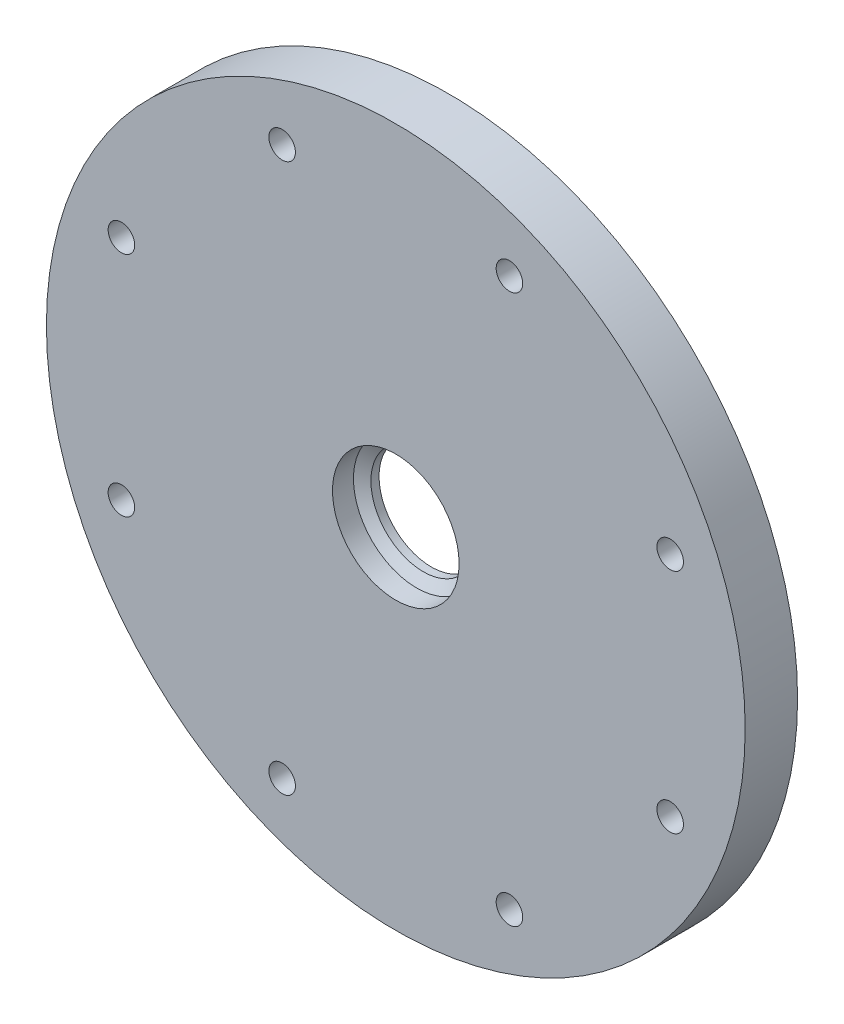
SolidWorks part; units mm, degrees
material "6061-T6 (SS)"
ref_plane "Front Plane" through (0, 0, 0) normal (0, 0, 1) x (1, 0, 0)
ref_plane "Top Plane" through (0, 0, 0) normal (0, 1, 0) x (1, 0, 0)
ref_plane "Right Plane" through (0, 0, 0) normal (1, 0, 0) x (0, 0, -1)
sketch "Sketch1" plane through (0, 0, 0) normal (0, 0, 1) x (1, 0, 0)
  circle A0 centre (0, 0) radius 9.525
  circle A2 centre (0, 0) radius 63.5
  dimension "D1" = 127
  dimension "D3" = 19.05
extrude "Boss-Extrude1" add sketch "Sketch1" along normal blind 9.525
sketch "Sketch4" plane through (0, 0, 9.525) normal (0, 0, 1) x (1, 0, 0)
  line L0 (49.8664, 20.6553) -> (58.6664, 24.3004) construction
  line L1 (0, 0) -> (63.5, 0) construction
  circle A0 centre (49.8664, 20.6553) radius 2.413
  circle A1 centre (0, 0) radius 63.5 construction
  dimension "D1" = 4.826
  dimension "D2" = 9.525
  dimension "D3" = 22.5
extrude "Cut-Extrude1" cut sketch "Sketch4" against normal through all
pattern_circular "CirPattern1" count 8 over 360 about axis through (0, 0, 0) along (0, 0, 1) of "Cut-Extrude1"
curve "Curve1"
  spline degree 3 poles (34.2959, 0, 0) (34.2988, 0.0719, 0) (34.3048, 0.2158, 0) (34.312, 0.4316, 0) (34.3179, 0.6476, 0) (34.3225, 0.8637, 0) (34.3258, 1.0798, 0) (34.3277, 1.296, 0) (34.3283, 1.5123, 0) (34.3275, 1.7287, 0) (34.3253, 1.9451, 0) (34.3218, 2.1615, 0) (34.317, 2.378, 0) (34.3108, 2.5945, 0) (34.3032, 2.811, 0) (34.2943, 3.0275, 0) (34.284, 3.2441, 0) (34.2724, 3.4606, 0) (34.2594, 3.6771, 0) (34.245, 3.8936, 0) (34.2293, 4.11, 0) (34.2122, 4.3264, 0) (34.1938, 4.5427, 0) (34.174, 4.759, 0) (34.1528, 4.9752, 0) (34.1303, 5.1914, 0) (34.1064, 5.4074, 0) (34.0811, 5.6234, 0) (34.0545, 5.8392, 0) (34.0265, 6.055, 0) (33.9972, 6.2706, 0) (33.9665, 6.4861, 0) (33.9344, 6.7015, 0) (33.901, 6.9167, 0) (33.8662, 7.1317, 0) (33.8301, 7.3466, 0) (33.7926, 7.5614, 0) (33.7537, 7.7759, 0) (33.7135, 7.9903, 0) (33.6719, 8.2044, 0) (33.629, 8.4184, 0) (33.5847, 8.6321, 0) (33.5391, 8.8456, 0) (33.4921, 9.0589, 0) (33.4438, 9.272, 0) (33.3941, 9.4848, 0) (33.343, 9.6973, 0) (33.2906, 9.9096, 0) (33.2369, 10.1216, 0) (33.1818, 10.3333, 0) (33.1254, 10.5447, 0) (33.0676, 10.7558, 0) (33.0085, 10.9666, 0) (32.9481, 11.1772, 0) (32.8863, 11.3873, 0) (32.8232, 11.5972, 0) (32.7587, 11.8067, 0) (32.6929, 12.0158, 0) (32.6258, 12.2246, 0) (32.5573, 12.433, 0) (32.4875, 12.6411, 0) (32.4164, 12.8487, 0) (32.344, 13.056, 0) (32.2702, 13.2629, 0) (32.1952, 13.4693, 0) (32.1188, 13.6754, 0) (32.0411, 13.881, 0) (31.9621, 14.0862, 0) (31.8817, 14.2909, 0) (31.8001, 14.4952, 0) (31.7172, 14.699, 0) (31.6329, 14.9023, 0) (31.5474, 15.1052, 0) (31.4605, 15.3076, 0) (31.3724, 15.5095, 0) (31.283, 15.7109, 0) (31.1923, 15.9118, 0) (31.1002, 16.1122, 0) (31.007, 16.312, 0) (30.9124, 16.5113, 0) (30.8165, 16.7101, 0) (30.7194, 16.9083, 0) (30.621, 17.1059, 0) (30.5214, 17.303, 0) (30.4205, 17.4995, 0) (30.3183, 17.6955, 0) (30.2148, 17.8908, 0) (30.1101, 18.0856, 0) (30.0042, 18.2797, 0) (29.897, 18.4732, 0) (29.7885, 18.6661, 0) (29.6788, 18.8583, 0) (29.5679, 19.05, 0) (29.4557, 19.2409, 0) (29.3424, 19.4313, 0) (29.2277, 19.6209, 0) (29.1119, 19.8099, 0) (28.9949, 19.9982, 0) (28.8766, 20.1858, 0) (28.7571, 20.3727, 0) (28.6364, 20.5589, 0) (28.5145, 20.7444, 0) (28.3914, 20.9292, 0) (28.2671, 21.1133, 0) (28.1417, 21.2966, 0) (28.015, 21.4792, 0) (27.8872, 21.661, 0) (27.7582, 21.8421, 0) (27.628, 22.0224, 0) (27.4966, 22.202, 0) (27.3641, 22.3807, 0) (27.2304, 22.5587, 0) (27.0956, 22.7359, 0) (26.9596, 22.9123, 0) (26.8225, 23.0879, 0) (26.6842, 23.2626, 0) (26.5448, 23.4365, 0) (26.4043, 23.6096, 0) (26.2626, 23.7819, 0) (26.1198, 23.9533, 0) (25.9759, 24.1239, 0) (25.8309, 24.2936, 0) (25.6848, 24.4624, 0) (25.5376, 24.6304, 0) (25.3893, 24.7974, 0) (25.2399, 24.9636, 0) (25.0894, 25.1289, 0) (24.9379, 25.2933, 0) (24.7852, 25.4568, 0) (24.6315, 25.6193, 0) (24.4768, 25.781, 0) (24.3209, 25.9417, 0) (24.1641, 26.1014, 0) (24.0062, 26.2602, 0) (23.8472, 26.4181, 0) (23.6872, 26.575, 0) (23.5262, 26.7309, 0) (23.3641, 26.8859, 0) (23.2011, 27.0399, 0) (23.037, 27.1929, 0) (22.8719, 27.3449, 0) (22.7058, 27.4959, 0) (22.5388, 27.6459, 0) (22.3707, 27.7949, 0) (22.2017, 27.9429, 0) (22.0317, 28.0899, 0) (21.8607, 28.2358, 0) (21.6887, 28.3806, 0) (21.5158, 28.5245, 0) (21.342, 28.6673, 0) (21.1672, 28.809, 0) (20.9915, 28.9497, 0) (20.8148, 29.0893, 0) (20.6372, 29.2278, 0) (20.4587, 29.3652, 0) (20.2793, 29.5016, 0) (20.099, 29.6368, 0) (19.9177, 29.771, 0) (19.7356, 29.9041, 0) (19.5526, 30.036, 0) (19.3688, 30.1668, 0) (19.184, 30.2965, 0) (18.9984, 30.4251, 0) (18.8119, 30.5526, 0) (18.6246, 30.6789, 0) (18.4365, 30.804, 0) (18.2475, 30.928, 0) (18.0576, 31.0509, 0) (17.867, 31.1725, 0) (17.6755, 31.2931, 0) (17.4833, 31.4124, 0) (17.2902, 31.5306, 0) (17.0963, 31.6475, 0) (16.9017, 31.7633, 0) (16.7062, 31.8779, 0) (16.51, 31.9913, 0) (16.3131, 32.1035, 0) (16.1153, 32.2145, 0) (15.9169, 32.3243, 0) (15.7176, 32.4328, 0) (15.5177, 32.5401, 0) (15.317, 32.6462, 0) (15.1156, 32.7511, 0) (14.9135, 32.8547, 0) (14.7107, 32.957, 0) (14.5072, 33.0582, 0) (14.303, 33.158, 0) (14.0981, 33.2566, 0) (13.8925, 33.354, 0) (13.6863, 33.4501, 0) (13.4794, 33.5449, 0) (13.2719, 33.6384, 0) (13.0637, 33.7306, 0) (12.8549, 33.8216, 0) (12.6455, 33.9112, 0) (12.4354, 33.9996, 0) (12.2247, 34.0867, 0) (12.0135, 34.1724, 0) (11.8016, 34.2569, 0) (11.5892, 34.3401, 0) (11.3761, 34.4219, 0) (11.1625, 34.5024, 0) (10.9484, 34.5816, 0) (10.7337, 34.6595, 0) (10.5184, 34.736, 0) (10.3026, 34.8112, 0) (10.0863, 34.885, 0) (9.8694, 34.9576, 0) (9.6521, 35.0287, 0) (9.4342, 35.0986, 0) (9.2158, 35.167, 0) (8.997, 35.2341, 0) (8.7777, 35.2999, 0) (8.5579, 35.3643, 0) (8.3376, 35.4273, 0) (8.1169, 35.4889, 0) (7.8957, 35.5492, 0) (7.6741, 35.6081, 0) (7.4521, 35.6656, 0) (7.2297, 35.7218, 0) (7.0068, 35.7765, 0) (6.7835, 35.8299, 0) (6.5599, 35.8819, 0) (6.3359, 35.9325, 0) (6.1114, 35.9817, 0) (5.8867, 36.0294, 0) (5.6615, 36.0758, 0) (5.436, 36.1208, 0) (5.2102, 36.1644, 0) (4.984, 36.2065, 0) (4.7575, 36.2473, 0) (4.5307, 36.2866, 0) (4.3036, 36.3245, 0) (4.0762, 36.361, 0) (3.8485, 36.3961, 0) (3.6205, 36.4297, 0) (3.3923, 36.462, 0) (3.1638, 36.4928, 0) (2.935, 36.5221, 0) (2.706, 36.55, 0) (2.4768, 36.5765, 0) (2.2473, 36.6016, 0) (2.0176, 36.6252, 0) (1.7877, 36.6474, 0) (1.5576, 36.6682, 0) (1.3274, 36.6875, 0) (1.0969, 36.7053, 0) (0.8663, 36.7217, 0) (0.6355, 36.7367, 0) (0.4045, 36.7502, 0) (0.1734, 36.7623, 0) (-0.0578, 36.7729, 0) (-0.2892, 36.782, 0) (-0.5207, 36.7897, 0) (-0.7523, 36.796, 0) (-0.9839, 36.8008, 0) (-1.2157, 36.8041, 0) (-1.4476, 36.806, 0) (-1.6795, 36.8064, 0) (-1.9115, 36.8054, 0) (-2.1435, 36.8029, 0) (-2.3756, 36.7989, 0) (-2.6077, 36.7935, 0) (-2.8399, 36.7866, 0) (-3.0721, 36.7783, 0) (-3.3042, 36.7684, 0) (-3.5364, 36.7572, 0) (-3.7686, 36.7444, 0) (-4.0007, 36.7302, 0) (-4.2328, 36.7145, 0) (-4.4649, 36.6974, 0) (-4.6969, 36.6788, 0) (-4.9289, 36.6587, 0) (-5.1608, 36.6372, 0) (-5.3926, 36.6142, 0) (-5.6243, 36.5897, 0) (-5.856, 36.5638, 0) (-6.0875, 36.5364, 0) (-6.319, 36.5076, 0) (-6.5503, 36.4772, 0) (-6.7815, 36.4455, 0) (-7.0125, 36.4122, 0) (-7.2434, 36.3775, 0) (-7.4741, 36.3413, 0) (-7.7047, 36.3037, 0) (-7.935, 36.2646, 0) (-8.1652, 36.224, 0) (-8.3952, 36.182, 0) (-8.625, 36.1385, 0) (-8.8546, 36.0936, 0) (-9.084, 36.0472, 0) (-9.3131, 35.9994, 0) (-9.542, 35.9501, 0) (-9.7706, 35.8993, 0) (-9.999, 35.8471, 0) (-10.2271, 35.7934, 0) (-10.4549, 35.7383, 0) (-10.6824, 35.6818, 0) (-10.9097, 35.6238, 0) (-11.1366, 35.5643, 0) (-11.3632, 35.5034, 0) (-11.5895, 35.4411, 0) (-11.8155, 35.3773, 0) (-12.0411, 35.3121, 0) (-12.2663, 35.2455, 0) (-12.4912, 35.1774, 0) (-12.7157, 35.1079, 0) (-12.9399, 35.0369, 0) (-13.1637, 34.9645, 0) (-13.387, 34.8907, 0) (-13.61, 34.8155, 0) (-13.8325, 34.7388, 0) (-14.0546, 34.6608, 0) (-14.2763, 34.5813, 0) (-14.4975, 34.5004, 0) (-14.7183, 34.418, 0) (-14.9386, 34.3343, 0) (-15.1585, 34.2492, 0) (-15.3778, 34.1626, 0) (-15.5967, 34.0747, 0) (-15.8151, 33.9853, 0) (-16.033, 33.8945, 0) (-16.2503, 33.8024, 0) (-16.4672, 33.7089, 0) (-16.6835, 33.6139, 0) (-16.8992, 33.5176, 0) (-17.1145, 33.4199, 0) (-17.3291, 33.3208, 0) (-17.5432, 33.2204, 0) (-17.7567, 33.1186, 0) (-17.9696, 33.0154, 0) (-18.1819, 32.9108, 0) (-18.3937, 32.8049, 0) (-18.6048, 32.6976, 0) (-18.8153, 32.5889, 0) (-19.0251, 32.479, 0) (-19.2343, 32.3676, 0) (-19.4429, 32.2549, 0) (-19.6508, 32.1409, 0) (-19.8581, 32.0255, 0) (-20.0646, 31.9088, 0) (-20.2705, 31.7908, 0) (-20.4757, 31.6714, 0) (-20.6802, 31.5507, 0) (-20.884, 31.4287, 0) (-21.0871, 31.3054, 0) (-21.2895, 31.1808, 0) (-21.4911, 31.0548, 0) (-21.692, 30.9276, 0) (-21.8921, 30.7991, 0) (-22.0915, 30.6692, 0) (-22.2901, 30.5381, 0) (-22.488, 30.4057, 0) (-22.685, 30.272, 0) (-22.8813, 30.1371, 0) (-23.0767, 30.0009, 0) (-23.2714, 29.8634, 0) (-23.4652, 29.7246, 0) (-23.6583, 29.5846, 0) (-23.8504, 29.4434, 0) (-24.0418, 29.3008, 0) (-24.2323, 29.1571, 0) (-24.4219, 29.0121, 0) (-24.6107, 28.8659, 0) (-24.7986, 28.7185, 0) (-24.9856, 28.5698, 0) (-25.1718, 28.4199, 0) (-25.357, 28.2689, 0) (-25.5413, 28.1166, 0) (-25.7247, 27.9631, 0) (-25.9073, 27.8084, 0) (-26.0888, 27.6525, 0) (-26.2695, 27.4955, 0) (-26.4492, 27.3372, 0) (-26.6279, 27.1778, 0) (-26.8057, 27.0173, 0) (-26.9825, 26.8555, 0) (-27.1584, 26.6927, 0) (-27.3333, 26.5286, 0) (-27.5071, 26.3634, 0) (-27.68, 26.1971, 0) (-27.8519, 26.0297, 0) (-28.0228, 25.8611, 0) (-28.1926, 25.6914, 0) (-28.3615, 25.5206, 0) (-28.5293, 25.3487, 0) (-28.696, 25.1757, 0) (-28.8618, 25.0016, 0) (-29.0264, 24.8264, 0) (-29.19, 24.6502, 0) (-29.3525, 24.4728, 0) (-29.514, 24.2944, 0) (-29.6744, 24.1149, 0) (-29.8337, 23.9344, 0) (-29.9918, 23.7528, 0) (-30.1489, 23.5702, 0) (-30.3049, 23.3865, 0) (-30.4598, 23.2018, 0) (-30.6135, 23.0161, 0) (-30.7661, 22.8294, 0) (-30.9176, 22.6417, 0) (-31.0679, 22.4529, 0) (-31.2171, 22.2632, 0) (-31.3651, 22.0725, 0) (-31.512, 21.8808, 0) (-31.6576, 21.6881, 0) (-31.8021, 21.4945, 0) (-31.9455, 21.2999, 0) (-32.0876, 21.1043, 0) (-32.2286, 20.9079, 0) (-32.3683, 20.7104, 0) (-32.5068, 20.5121, 0) (-32.6442, 20.3128, 0) (-32.7803, 20.1126, 0) (-32.9151, 19.9115, 0) (-33.0488, 19.7095, 0) (-33.1812, 19.5066, 0) (-33.3124, 19.3028, 0) (-33.4423, 19.0981, 0) (-33.5709, 18.8926, 0) (-33.6983, 18.6862, 0) (-33.8244, 18.4789, 0) (-33.9493, 18.2709, 0) (-34.0729, 18.0619, 0) (-34.1952, 17.8522, 0) (-34.3162, 17.6416, 0) (-34.4359, 17.4302, 0) (-34.5543, 17.2179, 0) (-34.6714, 17.0049, 0) (-34.7872, 16.7911, 0) (-34.9017, 16.5765, 0) (-35.0148, 16.3612, 0) (-35.1266, 16.1451, 0) (-35.2371, 15.9282, 0) (-35.3463, 15.7105, 0) (-35.4541, 15.4922, 0) (-35.5606, 15.273, 0) (-35.6657, 15.0532, 0) (-35.7694, 14.8326, 0) (-35.8718, 14.6114, 0) (-35.9728, 14.3894, 0) (-36.0725, 14.1667, 0) (-36.1708, 13.9434, 0) (-36.2677, 13.7194, 0) (-36.3632, 13.4947, 0) (-36.4573, 13.2694, 0) (-36.55, 13.0434, 0) (-36.6413, 12.8167, 0) (-36.7312, 12.5895, 0) (-36.8198, 12.3616, 0) (-36.9069, 12.1331, 0) (-36.9925, 11.9039, 0) (-37.0768, 11.6742, 0) (-37.1596, 11.4439, 0) (-37.241, 11.2131, 0) (-37.321, 10.9816, 0) (-37.3996, 10.7496, 0) (-37.4766, 10.517, 0) (-37.5523, 10.2839, 0) (-37.6265, 10.0503, 0) (-37.6993, 9.8161, 0) (-37.7705, 9.5814, 0) (-37.8404, 9.3462, 0) (-37.9088, 9.1105, 0) (-37.9757, 8.8743, 0) (-38.0411, 8.6377, 0) (-38.105, 8.4005, 0) (-38.1675, 8.1629, 0) (-38.2285, 7.9249, 0) (-38.2881, 7.6864, 0) (-38.3461, 7.4475, 0) (-38.4026, 7.2081, 0) (-38.4577, 6.9683, 0) (-38.5112, 6.7281, 0) (-38.5633, 6.4876, 0) (-38.6138, 6.2466, 0) (-38.6629, 6.0052, 0) (-38.7104, 5.7635, 0) (-38.7565, 5.5214, 0) (-38.801, 5.279, 0) (-38.844, 5.0362, 0) (-38.8855, 4.7931, 0) (-38.9254, 4.5497, 0) (-38.9639, 4.306, 0) (-39.0008, 4.0619, 0) (-39.0362, 3.8176, 0) (-39.0701, 3.573, 0) (-39.1024, 3.3281, 0) (-39.1332, 3.0829, 0) (-39.1624, 2.8375, 0) (-39.1902, 2.5919, 0) (-39.2163, 2.346, 0) (-39.241, 2.0998, 0) (-39.2641, 1.8535, 0) (-39.2856, 1.6069, 0) (-39.3056, 1.3602, 0) (-39.3241, 1.1133, 0) (-39.341, 0.8661, 0) (-39.3564, 0.6189, 0) (-39.3702, 0.3714, 0) (-39.3824, 0.1238, 0) (-39.3931, -0.1239, 0) (-39.4022, -0.3718, 0) (-39.4098, -0.6197, 0) (-39.4158, -0.8678, 0) (-39.4203, -1.116, 0) (-39.4232, -1.3643, 0) (-39.4245, -1.6126, 0) (-39.4243, -1.8611, 0) (-39.4225, -2.1096, 0) (-39.4191, -2.3581, 0) (-39.4142, -2.6067, 0) (-39.4077, -2.8553, 0) (-39.3996, -3.1039, 0) (-39.39, -3.3526, 0) (-39.3788, -3.6012, 0) (-39.366, -3.8499, 0) (-39.3517, -4.0985, 0) (-39.3358, -4.3471, 0) (-39.3183, -4.5957, 0) (-39.2993, -4.8442, 0) (-39.2787, -5.0926, 0) (-39.2565, -5.341, 0) (-39.2327, -5.5893, 0) (-39.2074, -5.8375, 0) (-39.1805, -6.0857, 0) (-39.1521, -6.3337, 0) (-39.122, -6.5816, 0) (-39.0904, -6.8294, 0) (-39.0573, -7.077, 0) (-39.0225, -7.3245, 0) (-38.9862, -7.5718, 0) (-38.9484, -7.819, 0) (-38.9089, -8.066, 0) (-38.8679, -8.3128, 0) (-38.8254, -8.5594, 0) (-38.7813, -8.8058, 0) (-38.7356, -9.0519, 0) (-38.6883, -9.2979, 0) (-38.6395, -9.5436, 0) (-38.5891, -9.7891, 0) (-38.5372, -10.0343, 0) (-38.4837, -10.2793, 0) (-38.4287, -10.524, 0) (-38.3721, -10.7683, 0) (-38.314, -11.0124, 0) (-38.2543, -11.2562, 0) (-38.193, -11.4997, 0) (-38.1302, -11.7429, 0) (-38.0659, -11.9857, 0) (-38, -12.2282, 0) (-37.9325, -12.4703, 0) (-37.8636, -12.712, 0) (-37.7931, -12.9534, 0) (-37.721, -13.1944, 0) (-37.6474, -13.435, 0) (-37.5723, -13.6752, 0) (-37.4956, -13.915, 0) (-37.4175, -14.1544, 0) (-37.3378, -14.3933, 0) (-37.2565, -14.6318, 0) (-37.1738, -14.8698, 0) (-37.0895, -15.1074, 0) (-37.0037, -15.3445, 0) (-36.9164, -15.5811, 0) (-36.8276, -15.8173, 0) (-36.7373, -16.0529, 0) (-36.6454, -16.288, 0) (-36.5521, -16.5226, 0) (-36.4573, -16.7567, 0) (-36.3609, -16.9902, 0) (-36.2631, -17.2232, 0) (-36.1638, -17.4556, 0) (-36.063, -17.6875, 0) (-35.9607, -17.9188, 0) (-35.8569, -18.1495, 0) (-35.7517, -18.3796, 0) (-35.6449, -18.6091, 0) (-35.5367, -18.8379, 0) (-35.4271, -19.0662, 0) (-35.3159, -19.2938, 0) (-35.2034, -19.5208, 0) (-35.0893, -19.7471, 0) (-34.9738, -19.9728, 0) (-34.8569, -20.1978, 0) (-34.7385, -20.4221, 0) (-34.6186, -20.6457, 0) (-34.4973, -20.8686, 0) (-34.3746, -21.0908, 0) (-34.2505, -21.3123, 0) (-34.1249, -21.5331, 0) (-33.9979, -21.7531, 0) (-33.8695, -21.9724, 0) (-33.7397, -22.191, 0) (-33.6085, -22.4087, 0) (-33.4758, -22.6257, 0) (-33.3418, -22.842, 0) (-33.2064, -23.0574, 0) (-33.0696, -23.272, 0) (-32.9314, -23.4858, 0) (-32.7918, -23.6988, 0) (-32.6508, -23.911, 0) (-32.5085, -24.1224, 0) (-32.3648, -24.3328, 0) (-32.2198, -24.5425, 0) (-32.0734, -24.7513, 0) (-31.9256, -24.9592, 0) (-31.7765, -25.1662, 0) (-31.626, -25.3724, 0) (-31.4743, -25.5776, 0) (-31.3211, -25.782, 0) (-31.1667, -25.9854, 0) (-31.0109, -26.1879, 0) (-30.8539, -26.3895, 0) (-30.6955, -26.5901, 0) (-30.5358, -26.7898, 0) (-30.3748, -26.9886, 0) (-30.2126, -27.1863, 0) (-30.049, -27.3831, 0) (-29.8842, -27.5789, 0) (-29.7181, -27.7738, 0) (-29.5507, -27.9676, 0) (-29.382, -28.1604, 0) (-29.2122, -28.3522, 0) (-29.041, -28.543, 0) (-28.8686, -28.7328, 0) (-28.695, -28.9215, 0) (-28.5201, -29.1092, 0) (-28.3441, -29.2958, 0) (-28.1668, -29.4813, 0) (-27.9882, -29.6658, 0) (-27.8085, -29.8492, 0) (-27.6276, -30.0315, 0) (-27.4455, -30.2128, 0) (-27.2622, -30.3929, 0) (-27.0777, -30.5719, 0) (-26.8921, -30.7498, 0) (-26.7053, -30.9266, 0) (-26.5173, -31.1022, 0) (-26.3282, -31.2767, 0) (-26.1379, -31.45, 0) (-25.9465, -31.6222, 0) (-25.7539, -31.7933, 0) (-25.5603, -31.9631, 0) (-25.3655, -32.1318, 0) (-25.1696, -32.2993, 0) (-24.9726, -32.4656, 0) (-24.7745, -32.6307, 0) (-24.5753, -32.7946, 0) (-24.3751, -32.9573, 0) (-24.1737, -33.1188, 0) (-23.9713, -33.279, 0) (-23.7679, -33.438, 0) (-23.5634, -33.5958, 0) (-23.3578, -33.7523, 0) (-23.1512, -33.9075, 0) (-22.9436, -34.0615, 0) (-22.735, -34.2142, 0) (-22.5253, -34.3657, 0) (-22.3147, -34.5158, 0) (-22.103, -34.6647, 0) (-21.8904, -34.8123, 0) (-21.6767, -34.9586, 0) (-21.4621, -35.1035, 0) (-21.2466, -35.2472, 0) (-21.03, -35.3895, 0) (-20.8126, -35.5305, 0) (-20.5942, -35.6702, 0) (-20.3748, -35.8085, 0) (-20.1545, -35.9454, 0) (-19.9334, -36.0811, 0) (-19.7113, -36.2153, 0) (-19.4883, -36.3482, 0) (-19.2644, -36.4797, 0) (-19.0396, -36.6099, 0) (-18.814, -36.7387, 0) (-18.5874, -36.866, 0) (-18.3601, -36.992, 0) (-18.1319, -37.1166, 0) (-17.9028, -37.2398, 0) (-17.6729, -37.3615, 0) (-17.4422, -37.4819, 0) (-17.2107, -37.6008, 0) (-16.9783, -37.7183, 0) (-16.7452, -37.8343, 0) (-16.5113, -37.9489, 0) (-16.2766, -38.0621, 0) (-16.0411, -38.1738, 0) (-15.8049, -38.2841, 0) (-15.5679, -38.3929, 0) (-15.3302, -38.5002, 0) (-15.0917, -38.6061, 0) (-14.8526, -38.7105, 0) (-14.6127, -38.8134, 0) (-14.3721, -38.9148, 0) (-14.1308, -39.0147, 0) (-13.8888, -39.1132, 0) (-13.6461, -39.2101, 0) (-13.4028, -39.3056, 0) (-13.1588, -39.3995, 0) (-12.9141, -39.4919, 0) (-12.6688, -39.5828, 0) (-12.4229, -39.6722, 0) (-12.1764, -39.76, 0) (-11.9292, -39.8463, 0) (-11.6814, -39.9311, 0) (-11.4331, -40.0143, 0) (-11.1841, -40.096, 0) (-10.9346, -40.1762, 0) (-10.6845, -40.2548, 0) (-10.4339, -40.3318, 0) (-10.1827, -40.4073, 0) (-9.931, -40.4812, 0) (-9.6787, -40.5536, 0) (-9.426, -40.6244, 0) (-9.1727, -40.6936, 0) (-8.9189, -40.7612, 0) (-8.6647, -40.8272, 0) (-8.4099, -40.8917, 0) (-8.1547, -40.9546, 0) (-7.8991, -41.0159, 0) (-7.643, -41.0755, 0) (-7.3864, -41.1336, 0) (-7.1294, -41.1901, 0) (-6.872, -41.245, 0) (-6.6142, -41.2983, 0) (-6.356, -41.3499, 0) (-6.0974, -41.4, 0) (-5.8385, -41.4484, 0) (-5.5791, -41.4952, 0) (-5.3194, -41.5404, 0) (-5.0594, -41.584, 0) (-4.799, -41.6259, 0) (-4.5383, -41.6663, 0) (-4.2773, -41.7049, 0) (-4.016, -41.742, 0) (-3.7543, -41.7774, 0) (-3.4924, -41.8112, 0) (-3.2302, -41.8433, 0) (-2.9678, -41.8738, 0) (-2.7051, -41.9026, 0) (-2.4421, -41.9298, 0) (-2.1789, -41.9554, 0) (-1.9155, -41.9793, 0) (-1.6519, -42.0015, 0) (-1.3881, -42.0221, 0) (-1.124, -42.041, 0) (-0.8598, -42.0583, 0) (-0.5954, -42.0739, 0) (-0.3309, -42.0878, 0) (-0.0662, -42.1001, 0) (0.1987, -42.1108, 0) (0.4636, -42.1197, 0) (0.7287, -42.127, 0) (0.9939, -42.1326, 0) (1.2592, -42.1366, 0) (1.5246, -42.1389, 0) (1.7901, -42.1395, 0) (2.0556, -42.1384, 0) (2.3212, -42.1357, 0) (2.5868, -42.1313, 0) (2.8525, -42.1252, 0) (3.1182, -42.1175, 0) (3.3839, -42.1081, 0) (3.6497, -42.097, 0) (3.9154, -42.0842, 0) (4.1811, -42.0697, 0) (4.4468, -42.0536, 0) (4.7124, -42.0358, 0) (4.978, -42.0163, 0) (5.2435, -41.9952, 0) (5.509, -41.9723, 0) (5.7744, -41.9478, 0) (6.0397, -41.9216, 0) (6.3049, -41.8938, 0) (6.5699, -41.8642, 0) (6.8349, -41.833, 0) (7.0997, -41.8001, 0) (7.3644, -41.7655, 0) (7.6289, -41.7293, 0) (7.8933, -41.6914, 0) (8.1575, -41.6518, 0) (8.4215, -41.6105, 0) (8.6853, -41.5676, 0) (8.9489, -41.5229, 0) (9.2123, -41.4767, 0) (9.4754, -41.4287, 0) (9.7383, -41.3791, 0) (10.001, -41.3278, 0) (10.2634, -41.2748, 0) (10.5256, -41.2202, 0) (10.7874, -41.1639, 0) (11.049, -41.106, 0) (11.3102, -41.0464, 0) (11.5712, -40.9851, 0) (11.8318, -40.9222, 0) (12.0921, -40.8576, 0) (12.3521, -40.7914, 0) (12.6116, -40.7235, 0) (12.8709, -40.6539, 0) (13.1297, -40.5827, 0) (13.3882, -40.5099, 0) (13.6463, -40.4354, 0) (13.9039, -40.3593, 0) (14.1612, -40.2815, 0) (14.418, -40.2021, 0) (14.6744, -40.1211, 0) (14.9303, -40.0384, 0) (15.1858, -39.9541, 0) (15.4408, -39.8682, 0) (15.6953, -39.7806, 0) (15.9493, -39.6914, 0) (16.2029, -39.6006, 0) (16.4559, -39.5082, 0) (16.7084, -39.4141, 0) (16.9604, -39.3185, 0) (17.2118, -39.2212, 0) (17.4627, -39.1224, 0) (17.713, -39.0219, 0) (17.9627, -38.9198, 0) (18.2119, -38.8161, 0) (18.4604, -38.7109, 0) (18.7084, -38.604, 0) (18.9557, -38.4956, 0) (19.2024, -38.3856, 0) (19.4485, -38.274, 0) (19.694, -38.1608, 0) (19.9388, -38.046, 0) (20.1829, -37.9297, 0) (20.4263, -37.8118, 0) (20.6691, -37.6924, 0) (20.9112, -37.5714, 0) (21.1526, -37.4488, 0) (21.3932, -37.3247, 0) (21.6331, -37.199, 0) (21.8723, -37.0718, 0) (22.1108, -36.9431, 0) (22.3485, -36.8128, 0) (22.5854, -36.6811, 0) (22.8216, -36.5477, 0) (23.057, -36.4129, 0) (23.2916, -36.2766, 0) (23.5253, -36.1387, 0) (23.7583, -35.9993, 0) (23.9905, -35.8585, 0) (24.2218, -35.7161, 0) (24.4523, -35.5723, 0) (24.6819, -35.4269, 0) (24.9107, -35.2801, 0) (25.1386, -35.1318, 0) (25.3656, -34.982, 0) (25.5917, -34.8308, 0) (25.8169, -34.6781, 0) (26.0412, -34.524, 0) (26.2647, -34.3684, 0) (26.4871, -34.2114, 0) (26.7087, -34.0529, 0) (26.9293, -33.893, 0) (27.1489, -33.7316, 0) (27.3676, -33.5689, 0) (27.5853, -33.4047, 0) (27.802, -33.2391, 0) (28.0178, -33.0722, 0) (28.2325, -32.9038, 0) (28.4462, -32.734, 0) (28.6589, -32.5628, 0) (28.8706, -32.3903, 0) (29.0812, -32.2164, 0) (29.2908, -32.0411, 0) (29.4994, -31.8644, 0) (29.7068, -31.6864, 0) (29.9133, -31.5071, 0) (30.1186, -31.3264, 0) (30.3228, -31.1444, 0) (30.526, -30.961, 0) (30.728, -30.7763, 0) (30.9289, -30.5903, 0) (31.1287, -30.403, 0) (31.3274, -30.2144, 0) (31.5249, -30.0245, 0) (31.7213, -29.8333, 0) (31.9165, -29.6409, 0) (32.1105, -29.4471, 0) (32.3034, -29.2521, 0) (32.4951, -29.0558, 0) (32.6856, -28.8583, 0) (32.8749, -28.6595, 0) (33.063, -28.4595, 0) (33.2499, -28.2582, 0) (33.4356, -28.0558, 0) (33.62, -27.8521, 0) (33.8032, -27.6472, 0) (33.9851, -27.4411, 0) (34.1658, -27.2338, 0) (34.3452, -27.0253, 0) (34.5234, -26.8156, 0) (34.7003, -26.6048, 0) (34.8759, -26.3928, 0) (35.0502, -26.1796, 0) (35.2232, -25.9653, 0) (35.3949, -25.7499, 0) (35.5652, -25.5333, 0) (35.7343, -25.3156, 0) (35.902, -25.0968, 0) (36.0684, -24.8769, 0) (36.2334, -24.6558, 0) (36.3971, -24.4337, 0) (36.5594, -24.2105, 0) (36.7204, -23.9863, 0) (36.8799, -23.7609, 0) (37.0381, -23.5345, 0) (37.195, -23.3071, 0) (37.3504, -23.0786, 0) (37.5044, -22.8491, 0) (37.657, -22.6185, 0) (37.8082, -22.387, 0) (37.9579, -22.1544, 0) (38.1063, -21.9208, 0) (38.2532, -21.6863, 0) (38.3986, -21.4508, 0) (38.5426, -21.2142, 0) (38.6852, -20.9768, 0) (38.8263, -20.7384, 0) (38.9659, -20.499, 0) (39.1041, -20.2587, 0) (39.2407, -20.0175, 0) (39.3759, -19.7753, 0) (39.5096, -19.5323, 0) (39.6418, -19.2883, 0) (39.7725, -19.0435, 0) (39.9017, -18.7977, 0) (40.0293, -18.5511, 0) (40.1554, -18.3037, 0) (40.2801, -18.0554, 0) (40.4031, -17.8062, 0) (40.5247, -17.5562, 0) (40.6446, -17.3054, 0) (40.7631, -17.0538, 0) (40.88, -16.8014, 0) (40.9953, -16.5482, 0) (41.109, -16.2941, 0) (41.2212, -16.0394, 0) (41.3318, -15.7838, 0) (41.4408, -15.5275, 0) (41.5482, -15.2704, 0) (41.6541, -15.0127, 0) (41.7583, -14.7541, 0) (41.8609, -14.4949, 0) (41.9619, -14.235, 0) (42.0614, -13.9743, 0) (42.1591, -13.713, 0) (42.2553, -13.451, 0) (42.3499, -13.1883, 0) (42.4428, -12.925, 0) (42.534, -12.661, 0) (42.6237, -12.3964, 0) (42.7117, -12.1312, 0) (42.798, -11.8653, 0) (42.8827, -11.5988, 0) (42.9657, -11.3318, 0) (43.0471, -11.0641, 0) (43.1268, -10.7959, 0) (43.2048, -10.5271, 0) (43.2811, -10.2578, 0) (43.3558, -9.9879, 0) (43.4288, -9.7175, 0) (43.5001, -9.4466, 0) (43.5697, -9.1751, 0) (43.6376, -8.9032, 0) (43.7039, -8.6307, 0) (43.7684, -8.3578, 0) (43.8312, -8.0844, 0) (43.8923, -7.8106, 0) (43.9517, -7.5363, 0) (44.0094, -7.2615, 0) (44.0654, -6.9864, 0) (44.1197, -6.7108, 0) (44.1722, -6.4348, 0) (44.223, -6.1584, 0) (44.2721, -5.8816, 0) (44.3194, -5.6045, 0) (44.365, -5.327, 0) (44.4089, -5.0491, 0) (44.4511, -4.7709, 0) (44.4915, -4.4924, 0) (44.5301, -4.2136, 0) (44.567, -3.9344, 0) (44.6022, -3.655, 0) (44.6356, -3.3752, 0) (44.6672, -3.0952, 0) (44.6971, -2.8149, 0) (44.7252, -2.5344, 0) (44.7516, -2.2536, 0) (44.7762, -1.9726, 0) (44.7991, -1.6914, 0) (44.8202, -1.4099, 0) (44.8395, -1.1283, 0) (44.857, -0.8465, 0) (44.8728, -0.5645, 0) (44.8869, -0.2823, 0) (44.8948, -0.0941, 0) (44.8987, 0, 0) knots 0 0 0 0 0.00087 0.001741 0.002611 0.003482 0.004354 0.005225 0.006097 0.006969 0.007841 0.008713 0.009586 0.010459 0.011332 0.012205 0.013079 0.013953 0.014827 0.015701 0.016576 0.017451 0.018326 0.019201 0.020077 0.020952 0.021828 0.022705 0.023581 0.024458 0.025335 0.026212 0.02709 0.027968 0.028845 0.029724 0.030602 0.031481 0.03236 0.033239 0.034119 0.034998 0.035878 0.036758 0.037639 0.038519 0.0394 0.040282 0.041163 0.042045 0.042927 0.043809 0.044691 0.045574 0.046457 0.04734 0.048223 0.049107 0.049991 0.050875 0.051759 0.052644 0.053529 0.054414 0.055299 0.056185 0.057071 0.057957 0.058843 0.05973 0.060616 0.061504 0.062391 0.063278 0.064166 0.065054 0.065943 0.066831 0.06772 0.068609 0.069499 0.070388 0.071278 0.072168 0.073058 0.073949 0.07484 0.075731 0.076622 0.077514 0.078405 0.079298 0.08019 0.081082 0.081975 0.082868 0.083762 0.084655 0.085549 0.086443 0.087337 0.088232 0.089127 0.090022 0.090917 0.091813 0.092709 0.093605 0.094501 0.095398 0.096294 0.097191 0.098089 0.098986 0.099884 0.100782 0.101681 0.102579 0.103478 0.104377 0.105276 0.106176 0.107076 0.107976 0.108876 0.109777 0.110678 0.111579 0.11248 0.113382 0.114284 0.115186 0.116088 0.116991 0.117894 0.118797 0.1197 0.120604 0.121508 0.122412 0.123316 0.124221 0.125126 0.126031 0.126936 0.127842 0.128748 0.129654 0.130561 0.131467 0.132374 0.133281 0.134189 0.135096 0.136004 0.136913 0.137821 0.13873 0.139639 0.140548 0.141457 0.142367 0.143277 0.144187 0.145098 0.146009 0.14692 0.147831 0.148742 0.149654 0.150566 0.151478 0.152391 0.153304 0.154217 0.15513 0.156044 0.156957 0.157872 0.158786 0.1597 0.160615 0.16153 0.162446 0.163361 0.164277 0.165193 0.16611 0.167026 0.167943 0.16886 0.169778 0.170695 0.171613 0.172531 0.17345 0.174369 0.175287 0.176207 0.177126 0.178046 0.178966 0.179886 0.180806 0.181727 0.182648 0.183569 0.184491 0.185413 0.186335 0.187257 0.18818 0.189102 0.190025 0.190949 0.191872 0.192796 0.19372 0.194645 0.195569 0.196494 0.197419 0.198345 0.19927 0.200196 0.201122 0.202049 0.202975 0.203902 0.204829 0.205757 0.206685 0.207613 0.208541 0.209469 0.210398 0.211327 0.212256 0.213186 0.214116 0.215046 0.215976 0.216906 0.217837 0.218768 0.2197 0.220631 0.221563 0.222495 0.223428 0.22436 0.225293 0.226226 0.22716 0.228093 0.229027 0.229961 0.230896 0.231831 0.232766 0.233701 0.234636 0.235572 0.236508 0.237444 0.238381 0.239318 0.240255 0.241192 0.24213 0.243067 0.244006 0.244944 0.245883 0.246821 0.247761 0.2487 0.24964 0.25058 0.25152 0.25246 0.253401 0.254342 0.255283 0.256225 0.257166 0.258108 0.259051 0.259993 0.260936 0.261879 0.262822 0.263766 0.26471 0.265654 0.266598 0.267543 0.268488 0.269433 0.270378 0.271324 0.27227 0.273216 0.274163 0.275109 0.276056 0.277004 0.277951 0.278899 0.279847 0.280795 0.281744 0.282693 0.283642 0.284591 0.285541 0.286491 0.287441 0.288391 0.289342 0.290293 0.291244 0.292196 0.293147 0.294099 0.295052 0.296004 0.296957 0.29791 0.298863 0.299817 0.300771 0.301725 0.302679 0.303634 0.304589 0.305544 0.306499 0.307455 0.308411 0.309367 0.310324 0.31128 0.312237 0.313195 0.314152 0.31511 0.316068 0.317027 0.317985 0.318944 0.319903 0.320862 0.321822 0.322782 0.323742 0.324703 0.325663 0.326624 0.327586 0.328547 0.329509 0.330471 0.331433 0.332396 0.333359 0.334322 0.335285 0.336249 0.337213 0.338177 0.339141 0.340106 0.341071 0.342036 0.343002 0.343967 0.344933 0.3459 0.346866 0.347833 0.3488 0.349768 0.350735 0.351703 0.352671 0.35364 0.354608 0.355577 0.356547 0.357516 0.358486 0.359456 0.360426 0.361397 0.362367 0.363339 0.36431 0.365282 0.366253 0.367226 0.368198 0.369171 0.370144 0.371117 0.37209 0.373064 0.374038 0.375012 0.375987 0.376962 0.377937 0.378912 0.379888 0.380864 0.38184 0.382816 0.383793 0.38477 0.385747 0.386725 0.387703 0.388681 0.389659 0.390637 0.391616 0.392595 0.393575 0.394554 0.395534 0.396514 0.397495 0.398476 0.399457 0.400438 0.401419 0.402401 0.403383 0.404366 0.405348 0.406331 0.407314 0.408298 0.409281 0.410265 0.411249 0.412234 0.413219 0.414204 0.415189 0.416174 0.41716 0.418146 0.419133 0.420119 0.421106 0.422093 0.423081 0.424069 0.425057 0.426045 0.427033 0.428022 0.429011 0.43 0.43099 0.43198 0.43297 0.43396 0.434951 0.435942 0.436933 0.437925 0.438916 0.439908 0.440901 0.441893 0.442886 0.443879 0.444873 0.445866 0.44686 0.447854 0.448849 0.449843 0.450838 0.451834 0.452829 0.453825 0.454821 0.455817 0.456814 0.457811 0.458808 0.459806 0.460803 0.461801 0.462799 0.463798 0.464797 0.465796 0.466795 0.467795 0.468795 0.469795 0.470795 0.471796 0.472797 0.473798 0.474799 0.475801 0.476803 0.477806 0.478808 0.479811 0.480814 0.481817 0.482821 0.483825 0.484829 0.485834 0.486838 0.487843 0.488849 0.489854 0.49086 0.491866 0.492873 0.493879 0.494886 0.495893 0.496901 0.497909 0.498917 0.499925 0.500933 0.501942 0.502951 0.503961 0.50497 0.50598 0.506991 0.508001 0.509012 0.510023 0.511034 0.512046 0.513057 0.51407 0.515082 0.516095 0.517107 0.518121 0.519134 0.520148 0.521162 0.522176 0.523191 0.524206 0.525221 0.526236 0.527252 0.528268 0.529284 0.5303 0.531317 0.532334 0.533351 0.534369 0.535387 0.536405 0.537423 0.538442 0.539461 0.54048 0.541499 0.542519 0.543539 0.54456 0.54558 0.546601 0.547622 0.548643 0.549665 0.550687 0.551709 0.552732 0.553755 0.554778 0.555801 0.556824 0.557848 0.558872 0.559897 0.560922 0.561947 0.562972 0.563997 0.565023 0.566049 0.567075 0.568102 0.569129 0.570156 0.571184 0.572211 0.573239 0.574268 0.575296 0.576325 0.577354 0.578383 0.579413 0.580443 0.581473 0.582503 0.583534 0.584565 0.585596 0.586628 0.58766 0.588692 0.589724 0.590757 0.59179 0.592823 0.593857 0.59489 0.595924 0.596959 0.597993 0.599028 0.600063 0.601099 0.602135 0.60317 0.604207 0.605243 0.60628 0.607317 0.608354 0.609392 0.61043 0.611468 0.612507 0.613545 0.614584 0.615624 0.616663 0.617703 0.618743 0.619784 0.620824 0.621865 0.622906 0.623948 0.62499 0.626032 0.627074 0.628117 0.629159 0.630203 0.631246 0.63229 0.633334 0.634378 0.635423 0.636467 0.637512 0.638558 0.639604 0.640649 0.641696 0.642742 0.643789 0.644836 0.645883 0.646931 0.647979 0.649027 0.650075 0.651124 0.652173 0.653222 0.654272 0.655322 0.656372 0.657422 0.658473 0.659524 0.660575 0.661626 0.662678 0.66373 0.664782 0.665835 0.666888 0.667941 0.668994 0.670048 0.671102 0.672156 0.673211 0.674266 0.675321 0.676376 0.677432 0.678488 0.679544 0.6806 0.681657 0.682714 0.683771 0.684829 0.685887 0.686945 0.688003 0.689062 0.690121 0.69118 0.69224 0.6933 0.69436 0.69542 0.696481 0.697542 0.698603 0.699665 0.700726 0.701788 0.702851 0.703913 0.704976 0.70604 0.707103 0.708167 0.709231 0.710295 0.71136 0.712424 0.71349 0.714555 0.715621 0.716687 0.717753 0.718819 0.719886 0.720953 0.722021 0.723088 0.724156 0.725224 0.726293 0.727362 0.728431 0.7295 0.73057 0.73164 0.73271 0.73378 0.734851 0.735922 0.736993 0.738065 0.739137 0.740209 0.741281 0.742354 0.743427 0.7445 0.745574 0.746647 0.747722 0.748796 0.749871 0.750945 0.752021 0.753096 0.754172 0.755248 0.756324 0.757401 0.758478 0.759555 0.760632 0.76171 0.762788 0.763867 0.764945 0.766024 0.767103 0.768183 0.769262 0.770342 0.771423 0.772503 0.773584 0.774665 0.775746 0.776828 0.77791 0.778992 0.780075 0.781158 0.782241 0.783324 0.784408 0.785492 0.786576 0.78766 0.788745 0.78983 0.790916 0.792001 0.793087 0.794173 0.79526 0.796346 0.797433 0.798521 0.799608 0.800696 0.801784 0.802873 0.803962 0.805051 0.80614 0.807229 0.808319 0.809409 0.8105 0.811591 0.812682 0.813773 0.814864 0.815956 0.817048 0.818141 0.819233 0.820326 0.82142 0.822513 0.823607 0.824701 0.825795 0.82689 0.827985 0.82908 0.830176 0.831271 0.832367 0.833464 0.83456 0.835657 0.836755 0.837852 0.83895 0.840048 0.841146 0.842245 0.843344 0.844443 0.845542 0.846642 0.847742 0.848842 0.849943 0.851044 0.852145 0.853247 0.854348 0.85545 0.856553 0.857655 0.858758 0.859861 0.860965 0.862068 0.863172 0.864277 0.865381 0.866486 0.867591 0.868697 0.869802 0.870908 0.872015 0.873121 0.874228 0.875335 0.876443 0.87755 0.878658 0.879767 0.880875 0.881984 0.883093 0.884202 0.885312 0.886422 0.887532 0.888643 0.889754 0.890865 0.891976 0.893088 0.8942 0.895312 0.896425 0.897538 0.898651 0.899764 0.900878 0.901992 0.903106 0.90422 0.905335 0.90645 0.907566 0.908681 0.909797 0.910914 0.91203 0.913147 0.914264 0.915381 0.916499 0.917617 0.918735 0.919854 0.920973 0.922092 0.923211 0.924331 0.925451 0.926571 0.927691 0.928812 0.929933 0.931055 0.932176 0.933298 0.934421 0.935543 0.936666 0.937789 0.938912 0.940036 0.94116 0.942284 0.943409 0.944533 0.945659 0.946784 0.94791 0.949036 0.950162 0.951288 0.952415 0.953542 0.95467 0.955797 0.956925 0.958053 0.959182 0.960311 0.96144 0.962569 0.963699 0.964829 0.965959 0.96709 0.968221 0.969352 0.970483 0.971615 0.972747 0.973879 0.975011 0.976144 0.977277 0.978411 0.979545 0.980678 0.981813 0.982947 0.984082 0.985217 0.986353 0.987488 0.988624 0.989761 0.990897 0.992034 0.993171 0.994309 0.995446 0.996584 0.997723 0.998861 1 1 1 1
sketch "Sketch7" plane through (0, 0, 0) normal (0, 0, 1) x (1, 0, 0)
  line L1 (41.7265, 3.3082) -> (38.3776, 3.3082)
  arc A0 (44.8987, 0) -> (41.7265, 3.3082) centre (41.7265, 0.1332) ccw
  arc A1 (38.3776, 3.3082) -> (35.2026, 0.1332) centre (38.3776, 0.1332) ccw
  arc A2 (35.2026, 0.1332) -> (34.2959, 0) centre (34.7619, -0.0192) cw
  arc A3 (38.3776, 3.3082) -> (33.8651, 7.1368) centre (38.3776, 7.8818) cw
  circle A4 centre (0, 0) radius 33.02
  spline S0 degree 3 poles (2030.2227, -117.7395) (22.7858, -27.2351) (33.8418, -13.6396) (34.312, 0.4316) (34.3179, 0.6476) (34.3271, 1.0799) (34.3329, 2.0903) (34.2799, 3.6074) (34.1204, 5.4103) (33.8802, 7.1353) (33.5529, 8.8499) (33.139, 10.5497) (32.6391, 12.2303) (32.0542, 13.8874) (31.3852, 15.5166) (30.6335, 17.1136) (29.8006, 18.6744) (28.8882, 20.1947) (27.8984, 21.6706) (26.8332, 23.098) (25.6951, 24.4731) (24.4865, 25.7922) (23.2102, 27.0516) (21.8693, 28.248) (20.4667, 29.3779) (19.0058, 30.4382) (17.49, 31.4258) (15.9229, 32.338) (14.3083, 33.1721) (12.6501, 33.9256) (10.9523, 34.5962) (9.219, 35.1819) (7.4546, 35.6807) (5.6632, 36.091) (3.8495, 36.4113) (2.0178, 36.6406) (0.1728, 36.7776) (-1.6809, 36.8217) (-3.5386, 36.7724) (-5.3955, 36.6294) (-7.2471, 36.3925) (-9.0884, 36.0621) (-10.9149, 35.6384) (-12.7217, 35.1223) (-14.5042, 34.5145) (-16.2577, 33.8162) (-17.9777, 33.0288) (-19.6596, 32.1539) (-21.2989, 31.1934) (-22.8914, 30.1492) (-24.4326, 29.0238) (-25.9186, 27.8195) (-27.3451, 26.5392) (-28.7085, 25.1857) (-30.0048, 23.7622) (-31.2305, 22.2719) (-32.3822, 20.7185) (-33.4566, 19.1055) (-34.4506, 17.4368) (-35.3613, 15.7165) (-36.1861, 13.9486) (-36.9225, 12.1375) (-37.5682, 10.2875) (-38.1211, 8.4034) (-38.5795, 6.4896) (-38.9418, 4.5509) (-39.2066, 2.5922) (-39.3728, 0.6184) (-39.4396, -1.3656) (-39.4064, -3.3547) (-39.2728, -5.3439) (-39.0387, -7.3282) (-38.7043, -9.3025) (-38.27, -11.2616) (-37.7365, -13.2006) (-37.1047, -15.1144) (-36.3758, -16.9979) (-35.5512, -18.8464) (-34.6327, -20.6549) (-33.6221, -22.4187) (-32.5217, -24.133) (-31.3338, -25.7933) (-30.0611, -27.3951) (-28.7065, -28.9341) (-27.273, -30.4061) (-25.7641, -31.807) (-24.1833, -33.133) (-22.5341, -34.3804) (-20.8206, -35.5457) (-19.0469, -36.6255) (-17.2172, -37.6168) (-15.3359, -38.5166) (-13.4077, -39.3222) (-11.4371, -40.0312) (-9.4292, -40.6415) (-7.3888, -41.1509) (-5.3209, -41.5579) (-3.2309, -41.8608) (-1.1238, -42.0586) (0.9951, -42.1502) (3.1203, -42.135) (5.2464, -42.0126) (7.3682, -41.7828) (9.4801, -41.4458) (11.5767, -41.002) (13.6527, -40.4521) (15.7025, -39.7969) (17.721, -39.0379) (19.7028, -38.1764) (21.6428, -37.2142) (23.5358, -36.1534) (25.3768, -34.9962) (27.1608, -33.7453) (28.8832, -32.4033) (30.5392, -30.9734) (32.1244, -29.4588) (33.6345, -27.8631) (35.0652, -26.19) (36.4127, -24.4433) (37.6731, -22.6273) (38.8428, -20.7464) (39.9186, -18.8049) (40.8973, -16.8077) (41.776, -14.7596) (42.552, -12.6656) (43.223, -10.5308) (43.7868, -8.3606) (44.2416, -6.1602) (44.5713, -4.0283) (44.7406, -2.4408) (44.8137, -1.5038) (44.8395, -1.1283) (44.857, -0.8465) (44.8728, -0.5645) (45.7077, 16.1379) (34.8318, 33.2748) (2044.1391, -40.8845) knots -0.167612 -0.167612 -0.167612 -0.167612 0.00087 0.001741 0.002611 0.003482 0.006969 0.014827 0.021828 0.028845 0.035878 0.042927 0.049991 0.057071 0.064166 0.071278 0.078405 0.085549 0.092709 0.099884 0.107076 0.114284 0.121508 0.128748 0.136004 0.143277 0.150566 0.157872 0.165193 0.172531 0.179886 0.187257 0.194645 0.202049 0.209469 0.216906 0.22436 0.231831 0.239318 0.246821 0.254342 0.261879 0.269433 0.277004 0.284591 0.292196 0.299817 0.307455 0.31511 0.322782 0.330471 0.338177 0.3459 0.35364 0.361397 0.369171 0.376962 0.38477 0.392595 0.400438 0.408298 0.416174 0.424069 0.43198 0.439908 0.447854 0.455817 0.463798 0.471796 0.479811 0.487843 0.495893 0.503961 0.512046 0.520148 0.528268 0.536405 0.54456 0.552732 0.560922 0.569129 0.577354 0.585596 0.593857 0.602135 0.61043 0.618743 0.627074 0.635423 0.643789 0.652173 0.660575 0.668994 0.677432 0.685887 0.69436 0.702851 0.71136 0.719886 0.728431 0.736993 0.745574 0.754172 0.762788 0.771423 0.780075 0.788745 0.797433 0.80614 0.814864 0.823607 0.832367 0.841146 0.849943 0.858758 0.867591 0.876443 0.885312 0.8942 0.903106 0.91203 0.920973 0.929933 0.938912 0.94791 0.956925 0.965959 0.975011 0.984082 0.992034 0.994309 0.995446 0.996584 0.997723 0.998861 1.198776 1.198776 1.198776 1.198776 only from (34.2959, 0) to (44.8987, 0) construction
  spline S1 degree 3 poles (34.2959, 0) (34.2988, 0.0719) (34.3048, 0.2158) (34.312, 0.4316) (34.3179, 0.6476) (34.3271, 1.0799) (34.3329, 2.0903) (34.2799, 3.6074) (34.1204, 5.4103) (33.8802, 7.1353) (33.5529, 8.8499) (33.139, 10.5497) (32.6391, 12.2303) (32.0542, 13.8874) (31.3852, 15.5166) (30.6335, 17.1136) (29.8006, 18.6744) (28.8882, 20.1947) (27.8984, 21.6706) (26.8332, 23.098) (25.6951, 24.4731) (24.4865, 25.7922) (23.2102, 27.0516) (21.8693, 28.248) (20.4667, 29.3779) (19.0058, 30.4382) (17.49, 31.4258) (15.9229, 32.338) (14.3083, 33.1721) (12.6501, 33.9256) (10.9523, 34.5962) (9.219, 35.1819) (7.4546, 35.6807) (5.6632, 36.091) (3.8495, 36.4113) (2.0178, 36.6406) (0.1728, 36.7776) (-1.6809, 36.8217) (-3.5386, 36.7724) (-5.3955, 36.6294) (-7.2471, 36.3925) (-9.0884, 36.0621) (-10.9149, 35.6384) (-12.7217, 35.1223) (-14.5042, 34.5145) (-16.2577, 33.8162) (-17.9777, 33.0288) (-19.6596, 32.1539) (-21.2989, 31.1934) (-22.8914, 30.1492) (-24.4326, 29.0238) (-25.9186, 27.8195) (-27.3451, 26.5392) (-28.7085, 25.1857) (-30.0048, 23.7622) (-31.2305, 22.2719) (-32.3822, 20.7185) (-33.4566, 19.1055) (-34.4506, 17.4368) (-35.3613, 15.7165) (-36.1861, 13.9486) (-36.9225, 12.1375) (-37.5682, 10.2875) (-38.1211, 8.4034) (-38.5795, 6.4896) (-38.9418, 4.5509) (-39.2066, 2.5922) (-39.3728, 0.6184) (-39.4396, -1.3656) (-39.4064, -3.3547) (-39.2728, -5.3439) (-39.0387, -7.3282) (-38.7043, -9.3025) (-38.27, -11.2616) (-37.7365, -13.2006) (-37.1047, -15.1144) (-36.3758, -16.9979) (-35.5512, -18.8464) (-34.6327, -20.6549) (-33.6221, -22.4187) (-32.5217, -24.133) (-31.3338, -25.7933) (-30.0611, -27.3951) (-28.7065, -28.9341) (-27.273, -30.4061) (-25.7641, -31.807) (-24.1833, -33.133) (-22.5341, -34.3804) (-20.8206, -35.5457) (-19.0469, -36.6255) (-17.2172, -37.6168) (-15.3359, -38.5166) (-13.4077, -39.3222) (-11.4371, -40.0312) (-9.4292, -40.6415) (-7.3888, -41.1509) (-5.3209, -41.5579) (-3.2309, -41.8608) (-1.1238, -42.0586) (0.9951, -42.1502) (3.1203, -42.135) (5.2464, -42.0126) (7.3682, -41.7828) (9.4801, -41.4458) (11.5767, -41.002) (13.6527, -40.4521) (15.7025, -39.7969) (17.721, -39.0379) (19.7028, -38.1764) (21.6428, -37.2142) (23.5358, -36.1534) (25.3768, -34.9962) (27.1608, -33.7453) (28.8832, -32.4033) (30.5392, -30.9734) (32.1244, -29.4588) (33.6345, -27.8631) (35.0652, -26.19) (36.4127, -24.4433) (37.6731, -22.6273) (38.8428, -20.7464) (39.9186, -18.8049) (40.8973, -16.8077) (41.776, -14.7596) (42.552, -12.6656) (43.223, -10.5308) (43.7868, -8.3606) (44.2416, -6.1602) (44.5713, -4.0283) (44.7406, -2.4408) (44.8137, -1.5038) (44.8395, -1.1283) (44.857, -0.8465) (44.8728, -0.5645) (44.8869, -0.2823) (44.8948, -0.0941) (44.8987, 0) knots 0 0 0 0 0.00087 0.001741 0.002611 0.003482 0.006969 0.014827 0.021828 0.028845 0.035878 0.042927 0.049991 0.057071 0.064166 0.071278 0.078405 0.085549 0.092709 0.099884 0.107076 0.114284 0.121508 0.128748 0.136004 0.143277 0.150566 0.157872 0.165193 0.172531 0.179886 0.187257 0.194645 0.202049 0.209469 0.216906 0.22436 0.231831 0.239318 0.246821 0.254342 0.261879 0.269433 0.277004 0.284591 0.292196 0.299817 0.307455 0.31511 0.322782 0.330471 0.338177 0.3459 0.35364 0.361397 0.369171 0.376962 0.38477 0.392595 0.400438 0.408298 0.416174 0.424069 0.43198 0.439908 0.447854 0.455817 0.463798 0.471796 0.479811 0.487843 0.495893 0.503961 0.512046 0.520148 0.528268 0.536405 0.54456 0.552732 0.560922 0.569129 0.577354 0.585596 0.593857 0.602135 0.61043 0.618743 0.627074 0.635423 0.643789 0.652173 0.660575 0.668994 0.677432 0.685887 0.69436 0.702851 0.71136 0.719886 0.728431 0.736993 0.745574 0.754172 0.762788 0.771423 0.780075 0.788745 0.797433 0.80614 0.814864 0.823607 0.832367 0.841146 0.849943 0.858758 0.867591 0.876443 0.885312 0.8942 0.903106 0.91203 0.920973 0.929933 0.938912 0.94791 0.956925 0.965959 0.975011 0.984082 0.992034 0.994309 0.995446 0.996584 0.997723 0.998861 1 1 1 1
  dimension "D2" = 3.175
  dimension "D4" = 66.04
  dimension "D1" = 0.9068
extrude "Boss-Extrude4" add sketch "Sketch7" against normal blind 4.826
sketch "Sketch9" plane through (0, 0, 0) normal (0, 0, -1) x (-1, 0, 0)
  circle A0 centre (0, 0) radius 33.02
  dimension "D1" = 66.04
extrude "Cut-Extrude2" cut sketch "Sketch9" against normal blind 3.048
hole_wizard "Pipe Tap Drill for 3/4 Tap4" positions "3DSketch1" profile "Sketch10" hole size "3/4" standard "ANSI Inch"
sketch3d "3DSketch1"
  point P0 (0, 0, 9.525)
sketch "Sketch10" plane through (0, 0, 9.525) normal (1, 0, 0) x (0, -1, 0)
  line L0 (0, 0) -> (0, 10.7236)
  line L1 (0, 10.7236) -> (11.5062, 3.81)
  line L2 (11.5062, 3.81) -> (11.5062, 0)
  line L5 (11.5062, 0) -> (0, 0)
  line L10 (0, 10.7236) -> (-11.5062, 3.81) construction
  line L11 (0, -6.35) -> (0, 107.95) construction
  dimension "Hole Dia." = 23.0124
  dimension "Hole Depth" = 3.81
  dimension "Drill Angle" = 118
